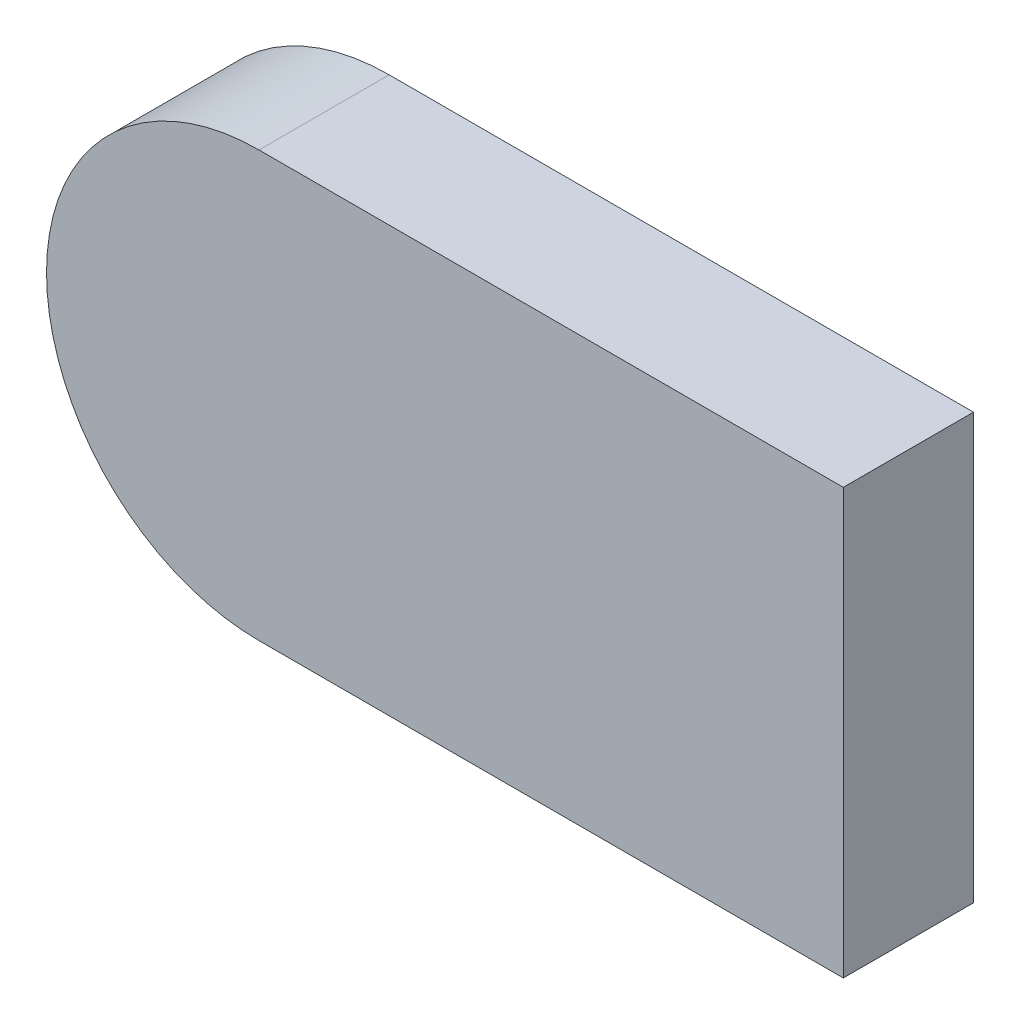
SolidWorks part; units mm, degrees
ref_plane "Front Plane" through (0, 0, 0) normal (0, 0, 1) x (1, 0, 0)
ref_plane "Top Plane" through (0, 0, 0) normal (0, 1, 0) x (1, 0, 0)
ref_plane "Right Plane" through (0, 0, 0) normal (1, 0, 0) x (0, 0, -1)
sketch "Sketch1" plane through (0, 0, 0) normal (0, 0, 1) x (1, 0, 0)
  line L1 (220, 57.5) -> (-80, 57.5)
  line L2 (220, 57.5) -> (220, -102.5)
  line L3 (220, -102.5) -> (-80, -102.5)
  line L4 (-80, 57.5) -> (-80, -102.5)
  arc A0 (190, -98.5) -> (190, 53.5) centre (108.7333, -22.5) ccw construction
  arc A1 (190, -98.5) -> (190, 53.5) centre (108.7333, -22.5) ccw construction
  arc A2 (-41.6241, 45.8186) -> (-41.6241, -90.8186) centre (0, -22.5) ccw construction
  arc A3 (-41.6241, 45.8186) -> (-41.6241, -90.8186) centre (0, -22.5) ccw
  arc A4 (-41.6241, -90.8186) -> (-41.6241, 45.8186) centre (0, -22.5) ccw construction
  arc A5 (-41.6241, -90.8186) -> (-41.6241, 45.8186) centre (0, -22.5) ccw
extrude "Boss-Extrude1" add sketch "Sketch1" against normal up to surface (49 mm away) contours A5 A3 | A5 L3 L2 L1
